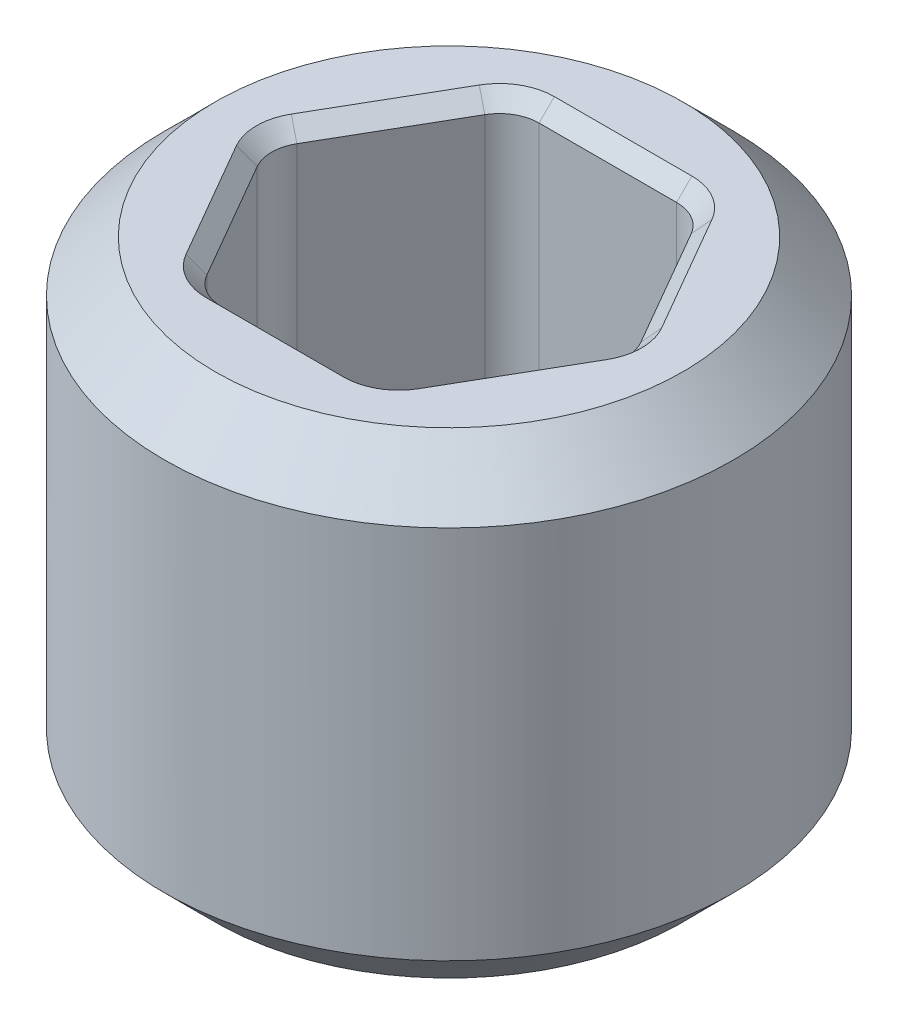
SolidWorks part; units mm, degrees
ref_plane "Front Plane" through (0, 0, 0) normal (0, 0, 1) x (1, 0, 0)
ref_plane "Top Plane" through (0, 0, 0) normal (0, 1, 0) x (1, 0, 0)
ref_plane "Right Plane" through (0, 0, 0) normal (1, 0, 0) x (0, 0, -1)
sketch "Sketch1" plane through (0, 0, 0) normal (0, 0, 1) x (1, 0, 0)
  line L0 (0, -1.7042) -> (0, -1.1626) construction
  line L1 (1.4224, -1.1906) -> (1.4224, 1.1906)
  line L2 (1.4224, 1.1906) -> (0, 1.1906)
  line L3 (0, 1.1906) -> (0, -1.1906)
  line L4 (0, -1.1906) -> (1.4224, -1.1906)
  dimension "D1" = 2.3813
  dimension "D2" = 2.8448
revolve "Revolve1" add sketch "Sketch1" angle 360 about L0
sketch "Sketch3" plane through (0, 0, 0) normal (0, 1, 0) x (1, 0, 0)
  line L1 (0.9165, 0) -> (0.4583, 0.7938)
  line L2 (0.4583, 0.7938) -> (-0.4583, 0.7937)
  line L3 (-0.4583, 0.7937) -> (-0.9165, 0)
  line L4 (-0.9165, 0) -> (-0.4583, -0.7938)
  line L5 (-0.4583, -0.7938) -> (0.4583, -0.7937)
  line L6 (0.4583, -0.7937) -> (0.9165, 0)
  circle A0 centre (0, 0) radius 0.7937 construction
  dimension "D1" = 1.5875
extrude "Cut-Extrude1" cut sketch "Sketch3" against normal through all both and the other way through all contours L2 L3 L4 L5 L6 L1
fillet "Fillet1" radius 0.1984 6 edges at (0.4583, 0, -0.7938) (0.9165, 0, 0) (0.4583, 0, 0.7937) (-0.4583, 0, 0.7938) (-0.9165, 0, 0) (-0.4583, 0, -0.7937)
chamfer "Chamfer1" distance 0.254 angle 45 2 edges at (0, -1.1906, -1.4224) (0, 1.1906, -1.4224)
chamfer "Chamfer2" distance 0.0762 angle 45 24 edges at (0.6874, 1.1906, -0.3969) (0.4429, 1.1906, -0.7672) (0.8858, 1.1906, 0) (0, 1.1906, -0.7937) (0.6874, 1.1906, 0.3969) (-0.4429, 1.1906, -0.7672) (0.4429, 1.1906, 0.7672) (-0.6874, 1.1906, -0.3969) (0, 1.1906, 0.7937) (-0.8858, 1.1906, 0) (-0.4429, 1.1906, 0.7672) (-0.6874, 1.1906, 0.3969) (0.6874, -1.1906, 0.3969) (0.8858, -1.1906, 0) (0.4429, -1.1906, 0.7672) (0.6874, -1.1906, -0.3969) (0, -1.1906, 0.7937) (0.4429, -1.1906, -0.7672) (-0.4429, -1.1906, 0.7672) (0, -1.1906, -0.7937) (-0.6874, -1.1906, 0.3969) (-0.4429, -1.1906, -0.7672) (-0.8858, -1.1906, 0) (-0.6874, -1.1906, -0.3969)
